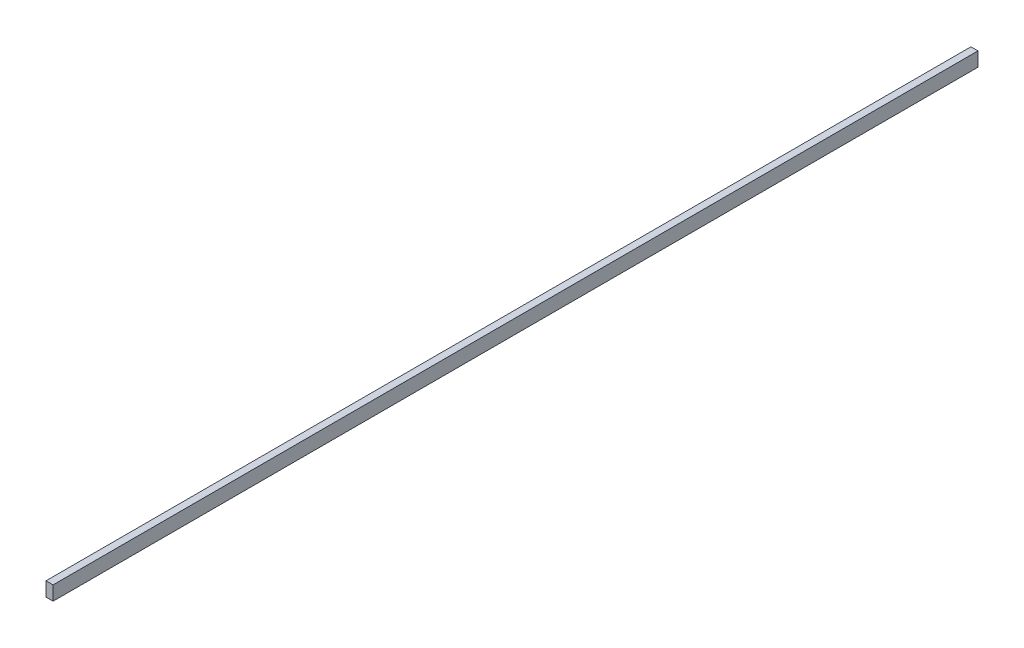
SolidWorks part; units mm, degrees
material "Balsa"
ref_plane "Front Plane" through (0, 0, 0) normal (0, 0, 1) x (1, 0, 0)
ref_plane "Top Plane" through (0, 0, 0) normal (0, 1, 0) x (1, 0, 0)
ref_plane "Right Plane" through (0, 0, 0) normal (1, 0, 0) x (0, 0, -1)
sketch "Sketch1" plane through (0, 0, 0) normal (0, 0, 1) x (1, 0, 0)
  line L1 (0, 0) -> (3.175, 0)
  line L2 (0, 0) -> (0, 6.35)
  line L3 (0, 6.35) -> (3.175, 6.35)
  line L4 (3.175, 0) -> (3.175, 6.35)
  dimension "D1" = 6.35
  dimension "D2" = 3.175
extrude "Boss-Extrude1" add sketch "Sketch1" along normal blind 415
